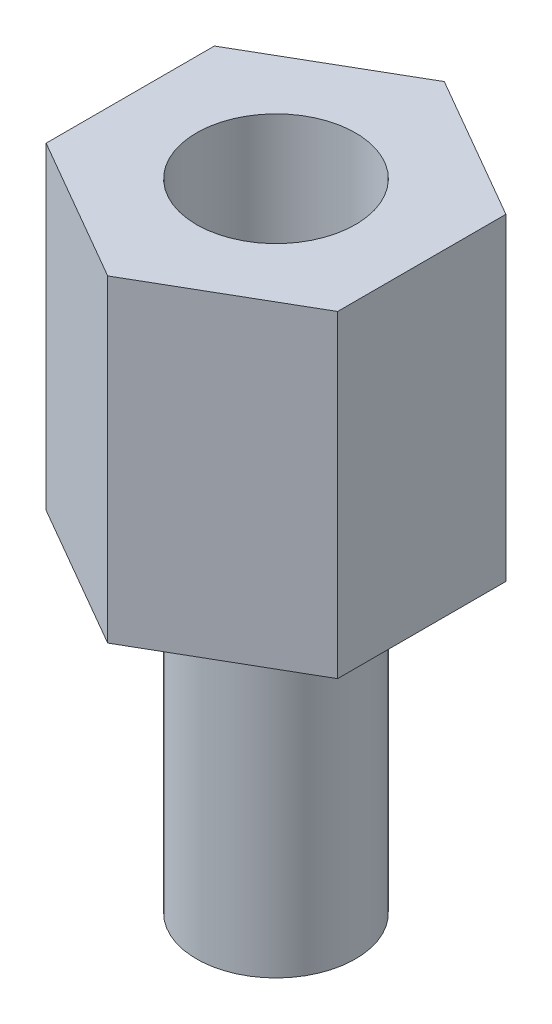
SolidWorks part; units mm, degrees
ref_plane "Alzado" through (0, 0, 0) normal (0, 0, 1) x (1, 0, 0)
ref_plane "Planta" through (0, 0, 0) normal (0, 1, 0) x (1, 0, 0)
ref_plane "Vista lateral" through (0, 0, 0) normal (1, 0, 0) x (0, 0, -1)
sketch "Croquis1" plane through (0, 0, 0) normal (0, 1, 0) x (1, 0, 0)
  line L1 (0, 3.1754) -> (-2.75, 1.5877)
  line L2 (-2.75, 1.5877) -> (-2.75, -1.5877)
  line L3 (-2.75, -1.5877) -> (0, -3.1754)
  line L4 (0, -3.1754) -> (2.75, -1.5877)
  line L5 (2.75, -1.5877) -> (2.75, 1.5877)
  line L6 (2.75, 1.5877) -> (0, 3.1754)
  circle A0 centre (0, 0) radius 2.75 construction
  dimension "D1" = 5.5
extrude "Saliente-Extruir1" add sketch "Croquis1" along normal blind 6
sketch "Croquis2" plane through (0, 0, 0) normal (0, -1, 0) x (1, 0, 0)
  circle A0 centre (0, 0) radius 1.5
  dimension "D1" = 3
extrude "Saliente-Extruir2" add sketch "Croquis2" along normal blind 6
sketch "Croquis3" plane through (0, 6, 0) normal (0, 1, 0) x (1, 0, 0)
  circle A0 centre (0, 0) radius 1.5
  dimension "D1" = 3
extrude "Cortar-Extruir1" cut sketch "Croquis3" against normal blind 5.5
